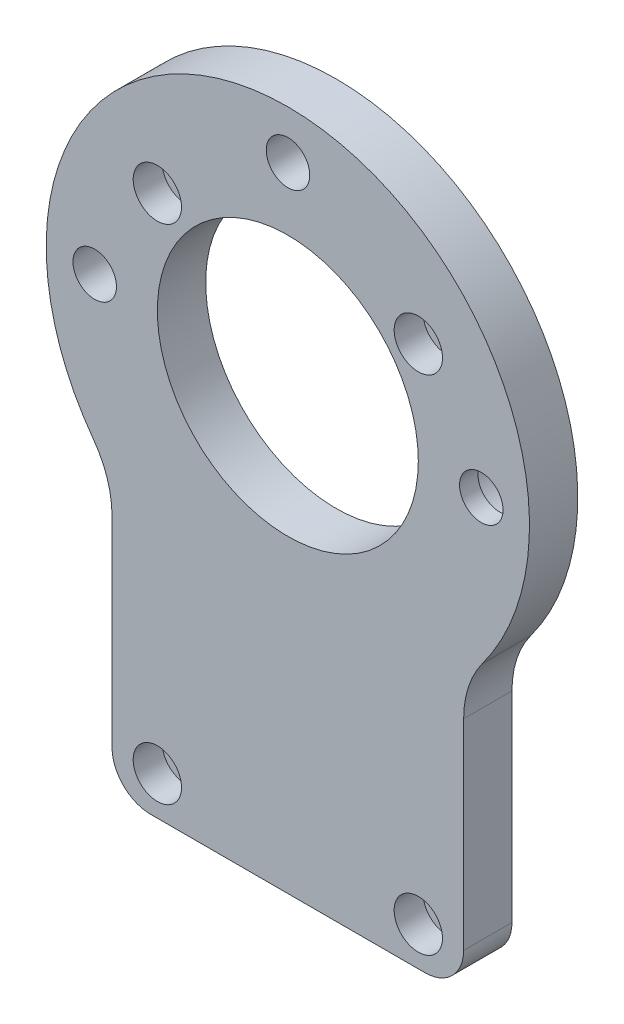
SolidWorks part; units mm, degrees
ref_plane "정면" through (0, 0, 0) normal (0, 0, 1) x (1, 0, 0)
ref_plane "윗면" through (0, 0, 0) normal (0, 1, 0) x (1, 0, 0)
ref_plane "우측면" through (0, 0, 0) normal (1, 0, 0) x (0, 0, -1)
sketch "스케치1" plane through (0, 0, 0) normal (0, 0, 1) x (1, 0, 0)
  line L0 (-13.5, 26) -> (13.5, -26) construction
  line L1 (-13.5, 26) -> (13.5, 26)
  line L2 (-13.5, 26) -> (-13.5, -5.5416)
  line L3 (-13.5, -26) -> (13.5, -26)
  line L4 (13.5, 26) -> (13.5, -5.5416)
  line L5 (13.5, 26) -> (-13.5, -26) construction
  line L6 (-13.5, -16.2) -> (-13.5, -26)
  line L7 (18.1886, -30) -> (-18.1886, -30)
  line L11 (25, -30) -> (-25, 30) construction
  line L12 (25, 30) -> (-25, -30) construction
  line L14 (18.1886, -5.2461) -> (18.1886, -26)
  line L15 (14.1886, -30) -> (-14.1886, -30)
  line L16 (-18.1886, -5.2461) -> (-18.1886, -26)
  line L17 (18.1886, 30) -> (-18.1886, -30) construction
  line L18 (18.1886, -30) -> (-13.5, 22.2667) construction
  line L19 (13.5, -16.2) -> (13.5, -26)
  circle A1 centre (-13.5, 26) radius 1.2
  circle A2 centre (13.5, 26) radius 1.2
  circle A3 centre (-13.5, -26) radius 1.2
  circle A4 centre (13.5, -26) radius 1.2
  circle A5 centre (0, 15.5) radius 13.5
  arc A6 (22.3328, 26.7993) -> (22.2628, 26.874) centre (15, 20) ccw
  arc A7 (-22.2628, 26.874) -> (-22.3328, 26.7993) centre (-15, 20) ccw
  arc A8 (-13.5, -5.5416) -> (13.5, -5.5416) centre (0, 15.5) ccw
  arc A9 (18.1886, -26) -> (14.1886, -30) centre (14.1886, -26) cw
  arc A10 (-14.1886, -30) -> (-18.1886, -26) centre (-14.1886, -26) cw
  arc A11 (20.1347, 0.6814) -> (-20.1347, 0.6814) centre (0, 15.5) ccw
  arc A12 (18.1886, -5.2461) -> (20.1347, 0.6814) centre (28.1886, -5.2461) cw
  arc A13 (-18.1886, -5.2461) -> (-20.1347, 0.6814) centre (-28.1886, -5.2461) ccw
  point P4 (0, 0)
  point P5 (0, 0)
  point P11 (0, 0)
  point P18 (0, 0)
  point P43 (18.1886, -1.6515)
  dimension "D3" = 2.4
  dimension "D4" = 2.4
  dimension "D5" = 2.4
  dimension "D6" = 2.4
  dimension "D9" = 10.5
  dimension "D11" = 27
  dimension "D12" = 10
  dimension "D13" = 4
  dimension "D14" = 10
  dimension "D1" = 52
  dimension "D2" = 27
  dimension "D7" = 60
  dimension "D8" = 50
  dimension "D10" = 13.5
extrude "보스-돌출1" add sketch "스케치1" along normal blind 5
sketch "스케치2" plane through (0, 0, 5) normal (0, 0, 1) x (1, 0, 0)
  circle A0 centre (-13.5, 26) radius 2.5
  circle A1 centre (13.5, 26) radius 2.5
  circle A2 centre (-13.5, -26) radius 2.5
  circle A3 centre (13.5, -26) radius 2.5
extrude "컷-돌출1" cut sketch "스케치2" against normal blind 3
sketch "스케치3" plane through (0, 0, 5) normal (0, 0, 1) x (1, 0, 0)
  line L0 (-1000, 0) -> (49000, 0) construction
  line L1 (0, -1000) -> (0, 49000) construction
  line L3 (0.0172, 15.5) -> (-19.9828, 15.5) construction
  line L4 (0.0172, 15.5) -> (0.0172, 35.5) construction
  circle A4 centre (-19.9828, 15.5) radius 2.25
  circle A5 centre (0.0172, 35.5) radius 2.25
  circle A6 centre (20.0172, 15.5) radius 2.25 construction
  point P15 (0, 15.5)
  dimension "D1" = 3
  dimension "D3" = 4.5
  dimension "D2" = 90
  dimension "D4" = 20
extrude "컷-돌출2" cut sketch "스케치3" against normal through all both and the other way through all
hole_wizard "M4 남비 머리 나사용 카운터보어2" positions "스케치7" profile "스케치8" counterbore size "M4" standard "ISO" end condition through all
sketch "스케치7" plane through (0, 0, 0) normal (0, 0, -1) x (-1, 0, 0)
  point P0 (-20.0172, 15.5)
sketch "스케치8" plane through (20.0172, 15.5, 0) normal (1, 0, 0) x (0, 1, 0)
  line L0 (0, 0) -> (0, 5)
  line L1 (0, 5) -> (2.25, 5)
  line L3 (2.25, 5) -> (2.25, 3.1)
  line L4 (2.25, 3.1) -> (4.5, 3.1)
  line L5 (4.5, 3.1) -> (4.5, 0)
  line L7 (4.5, 0) -> (0, 0)
  line L11 (0, -6.35) -> (0, 107.95) construction
  dimension "관통 구멍 지름" = 4.5
  dimension "관통 구멍 깊이" = 5
  dimension "카운터보어 지름" = 9
  dimension "카운터보어 깊이" = 3.1
